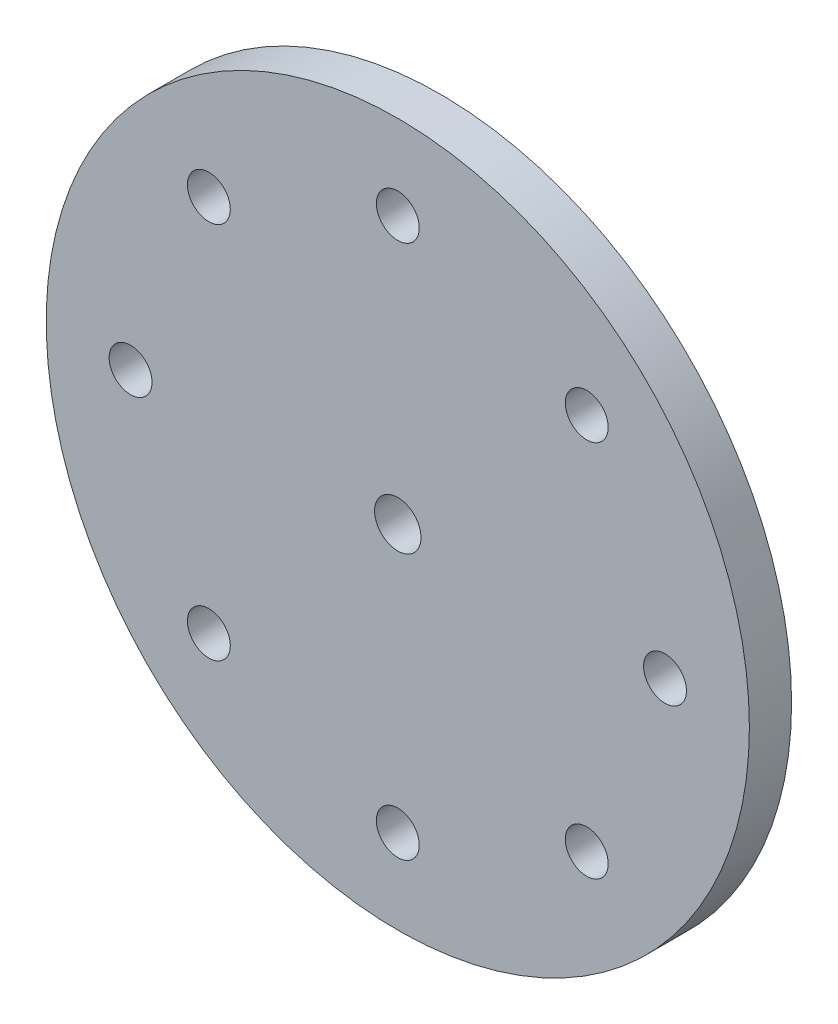
SolidWorks part; units mm, degrees
material "6061 合金"
ref_plane "前视基准面" through (0, 0, 0) normal (0, 0, 1) x (1, 0, 0)
ref_plane "上视基准面" through (0, 0, 0) normal (0, 1, 0) x (1, 0, 0)
ref_plane "右视基准面" through (0, 0, 0) normal (1, 0, 0) x (0, 0, -1)
sketch "草图1" plane through (0, 0, 0) normal (0, 0, 1) x (1, 0, 0)
  circle A0 centre (0, 0) radius 25
  circle A1 centre (0, 0) radius 19 construction
  circle A2 centre (0, 19) radius 1.525
  circle A3 centre (13.435, 13.435) radius 1.525
  circle A4 centre (19, 0) radius 1.525
  circle A5 centre (13.435, -13.435) radius 1.525
  circle A6 centre (0, -19) radius 1.525
  circle A7 centre (-13.435, -13.435) radius 1.525
  circle A8 centre (-19, 0) radius 1.525
  circle A9 centre (-13.435, 13.435) radius 1.525
  point P23 (0, 0)
  dimension "D1" = 50
  dimension "D2" = 38
  dimension "D3" = 3.05
  dimension "D4" = 8
extrude "凸台-拉伸1" add sketch "草图1" along normal blind 3
sketch "草图2" plane through (0, 0, 3) normal (0, 0, 1) x (1, 0, 0)
  circle A0 centre (0, 0) radius 4
  dimension "D1" = 8
extrude "凸台-拉伸2" add sketch "草图2" against normal blind 11.3 from surface at -3 starting at face at (25, 0, 0)
sketch "草图3" plane through (0, 0, 3) normal (0, 0, 1) x (1, 0, 0)
  circle A0 centre (0, 0) radius 5.2
  circle A1 centre (0, 0) radius 4 construction
  dimension "D1" = 1.2
extrude "凸台-拉伸3" add sketch "草图3" against normal blind 1.2 from surface at -3 starting at face at (4, 0, 0)
hole_wizard "M4 螺纹孔1" positions "草图4" profile "草图5" tap size "M4" standard "GB" end condition through all
sketch "草图4" plane through (0, 0, -11.3) normal (0, 0, -1) x (-1, 0, 0)
  point P0 (0, 0)
sketch "草图5" plane through (0, 0, -11.3) normal (1, 0, 0) x (0, 1, 0)
  line L0 (0, 0) -> (0, 14.3)
  line L1 (0, 14.3) -> (1.65, 14.3)
  line L2 (1.65, 14.3) -> (1.65, 0)
  line L5 (1.65, 0) -> (0, 0)
  line L11 (0, -6.35) -> (0, 107.95) construction
  dimension "通孔螺纹孔钻头直径" = 3.3
  dimension "通孔螺纹孔钻头深度" = 14.3
cosmetic thread "孔螺蚊线1" parameters "D2"=4
sketch "草图6" plane through (0, 0, 0) normal (0, 1, 0) x (1, 0, 0)
  line L0 (4, 11.3) -> (-4, 11.3) construction
  line L1 (-5, 11.3) -> (4, 11.3)
  line L2 (-5, 11.3) -> (-5, 9.2)
  line L3 (-5, 9.2) -> (4, 9.2)
  line L4 (4, 11.3) -> (4, 9.2)
  line L5 (4, 1.2) -> (4, 11.3) construction
  dimension "D1" = 2.1
  dimension "D2" = 9
extrude "切除-拉伸1" cut sketch "草图6" against normal through all both and the other way through all
